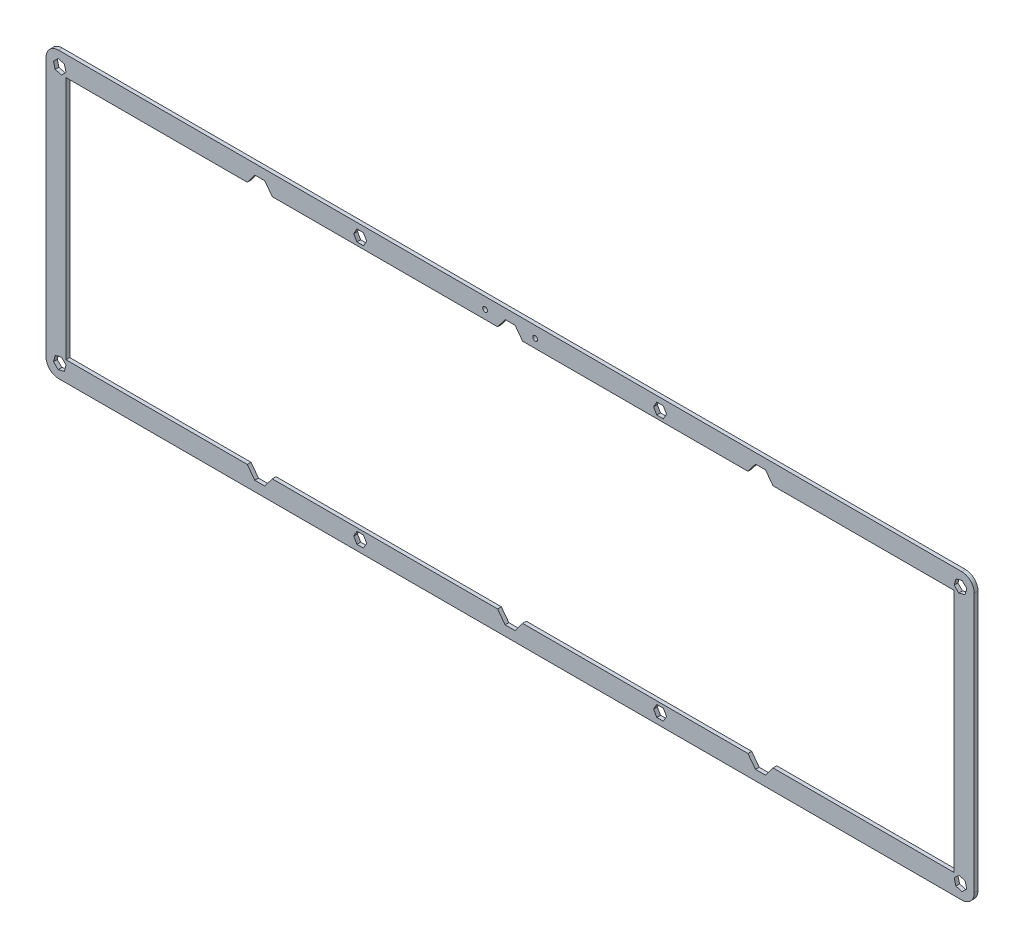
SolidWorks part; units mm, degrees
ref_plane "Front Plane" through (0, 0, 0) normal (0, 0, 1) x (1, 0, 0)
ref_plane "Top Plane" through (0, 0, 0) normal (0, 1, 0) x (1, 0, 0)
ref_plane "Right Plane" through (0, 0, 0) normal (1, 0, 0) x (0, 0, -1)
sketch "Model" plane through (0, 0, 0) normal (0, 0, 1) x (1, 0, 0)
  line L0 (0, 108.6) -> (0, 5)
  line L1 (365.775, 0) -> (5, 0)
  line L2 (370.775, 108.6) -> (370.775, 5)
  line L3 (365.775, 113.6) -> (5, 113.6)
  line L4 (8, 8) -> (8, 105.6)
  line L5 (362.775, 8) -> (362.775, 105.6)
  line L6 (8, 105.6) -> (80.3875, 105.6)
  line L7 (90.3875, 105.6) -> (180.3875, 105.6)
  line L8 (280.3875, 105.6) -> (283.3875, 109.6)
  line L9 (283.3875, 109.6) -> (287.3875, 109.6)
  line L10 (290.3875, 105.6) -> (287.3875, 109.6)
  line L11 (362.775, 105.6) -> (290.3875, 105.6)
  line L12 (280.3875, 105.6) -> (190.3875, 105.6)
  line L13 (8, 8) -> (80.3875, 8)
  line L14 (90.3875, 8) -> (180.3875, 8)
  line L15 (362.775, 8) -> (290.3875, 8)
  line L16 (280.3875, 8) -> (190.3875, 8)
  line L17 (180.3875, 105.6) -> (183.3875, 109.6)
  line L18 (183.3875, 109.6) -> (187.3875, 109.6)
  line L19 (190.3875, 105.6) -> (187.3875, 109.6)
  line L20 (80.3875, 105.6) -> (83.3875, 109.6)
  line L21 (83.3875, 109.6) -> (87.3875, 109.6)
  line L22 (90.3875, 105.6) -> (87.3875, 109.6)
  line L23 (280.3875, 8) -> (283.3875, 4)
  line L24 (283.3875, 4) -> (287.3875, 4)
  line L25 (290.3875, 8) -> (287.3875, 4)
  line L26 (180.3875, 8) -> (183.3875, 4)
  line L27 (183.3875, 4) -> (187.3875, 4)
  line L28 (190.3875, 8) -> (187.3875, 4)
  line L29 (80.3875, 8) -> (83.3875, 4)
  line L30 (83.3875, 4) -> (87.3875, 4)
  line L31 (90.3875, 8) -> (87.3875, 4)
  line L32 (365.9474, 110.6095) -> (367.7845, 108.7724)
  line L33 (367.7845, 108.7724) -> (367.1121, 106.2629)
  line L34 (367.1121, 106.2629) -> (364.6026, 105.5905)
  line L35 (364.6026, 105.5905) -> (362.7655, 107.4276)
  line L36 (362.7655, 107.4276) -> (363.4379, 109.9371)
  line L37 (363.4379, 109.9371) -> (365.9474, 110.6095)
  line L38 (4.8276, 110.6095) -> (2.9905, 108.7724)
  line L39 (2.9905, 108.7724) -> (3.6629, 106.2629)
  line L40 (3.6629, 106.2629) -> (6.1724, 105.5905)
  line L41 (6.1724, 105.5905) -> (8.0095, 107.4276)
  line L42 (8.0095, 107.4276) -> (7.3371, 109.9371)
  line L43 (7.3371, 109.9371) -> (4.8276, 110.6095)
  line L44 (365.9474, 2.9905) -> (367.7845, 4.8276)
  line L45 (367.7845, 4.8276) -> (367.1121, 7.3371)
  line L46 (367.1121, 7.3371) -> (364.6026, 8.0095)
  line L47 (364.6026, 8.0095) -> (362.7655, 6.1724)
  line L48 (362.7655, 6.1724) -> (363.4379, 3.6629)
  line L49 (363.4379, 3.6629) -> (365.9474, 2.9905)
  line L50 (126.799, 2.25) -> (124.201, 2.25)
  line L51 (124.201, 2.25) -> (122.9019, 4.5)
  line L52 (122.9019, 4.5) -> (124.201, 6.75)
  line L53 (124.201, 6.75) -> (126.799, 6.75)
  line L54 (126.799, 6.75) -> (128.0981, 4.5)
  line L55 (128.0981, 4.5) -> (126.799, 2.25)
  line L56 (4.8276, 2.9905) -> (2.9905, 4.8276)
  line L57 (2.9905, 4.8276) -> (3.6629, 7.3371)
  line L58 (3.6629, 7.3371) -> (6.1724, 8.0095)
  line L59 (6.1724, 8.0095) -> (8.0095, 6.1724)
  line L60 (8.0095, 6.1724) -> (7.3371, 3.6629)
  line L61 (7.3371, 3.6629) -> (4.8276, 2.9905)
  line L62 (243.976, 2.25) -> (246.574, 2.25)
  line L63 (246.574, 2.25) -> (247.8731, 4.5)
  line L64 (247.8731, 4.5) -> (246.574, 6.75)
  line L65 (246.574, 6.75) -> (243.976, 6.75)
  line L66 (243.976, 6.75) -> (242.6769, 4.5)
  line L67 (242.6769, 4.5) -> (243.976, 2.25)
  line L68 (126.799, 111.35) -> (124.201, 111.35)
  line L69 (124.201, 111.35) -> (122.9019, 109.1)
  line L70 (122.9019, 109.1) -> (124.201, 106.85)
  line L71 (124.201, 106.85) -> (126.799, 106.85)
  line L72 (126.799, 106.85) -> (128.0981, 109.1)
  line L73 (128.0981, 109.1) -> (126.799, 111.35)
  line L74 (243.976, 111.35) -> (246.574, 111.35)
  line L75 (246.574, 111.35) -> (247.8731, 109.1)
  line L76 (247.8731, 109.1) -> (246.574, 106.85)
  line L77 (246.574, 106.85) -> (243.976, 106.85)
  line L78 (243.976, 106.85) -> (242.6769, 109.1)
  line L79 (242.6769, 109.1) -> (243.976, 111.35)
  arc A0 (365.775, 0) -> (370.775, 5) centre (365.775, 5) ccw
  arc A1 (370.775, 108.6) -> (365.775, 113.6) centre (365.775, 108.6) ccw
  arc A2 (0, 5) -> (5, 0) centre (5, 5) ccw
  arc A3 (5, 113.6) -> (0, 108.6) centre (5, 108.6) ccw
  circle A4 centre (175.3875, 109.1) radius 0.95
  circle A5 centre (195.3875, 109.1) radius 0.95
  dimension "D2" = 1.9
  dimension "D3" = 1.9
  dimension "D1" = 113.6
  dimension "D4" = 8
  dimension "D5" = 8
extrude "Boss-Extrude1" add sketch "Model" along normal blind 1.5
